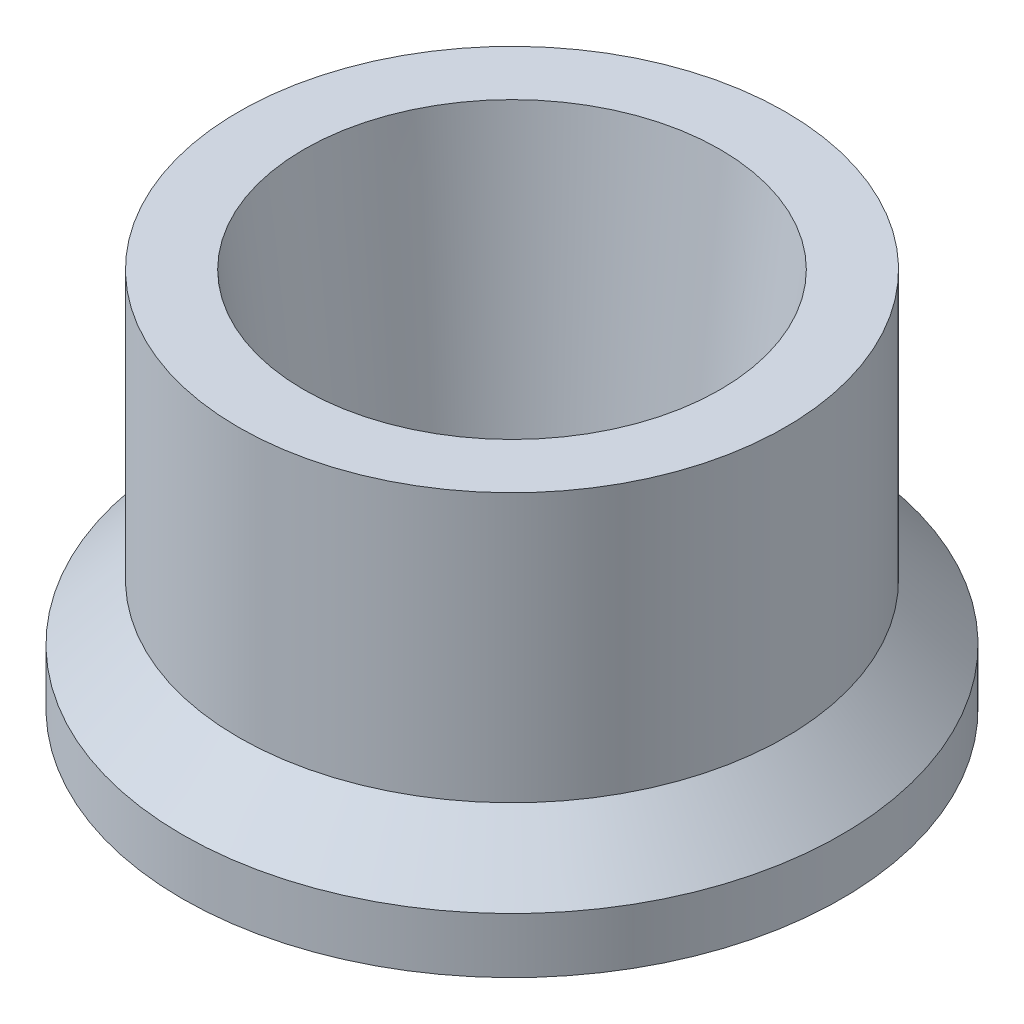
SolidWorks part; units mm, degrees
material "1060 Alloy"
ref_plane "Front" through (0, 0, 0) normal (0, 0, 1) x (1, 0, 0)
ref_plane "Top" through (0, 0, 0) normal (0, 1, 0) x (1, 0, 0)
ref_plane "Right" through (0, 0, 0) normal (1, 0, 0) x (0, 0, -1)
sketch "Sketch1" plane through (0, 0, 0) normal (0, 0, 1) x (1, 0, 0)
  line L0 (3.048, 0) -> (3.81, 6.9596)
  line L1 (50, 0) -> (-50, 0) construction
  line L2 (3.81, 6.9596) -> (5.0038, 6.9596)
  line L3 (5.0038, 6.9596) -> (5.0038, 2.0447)
  line L4 (5.0038, 2.0447) -> (6.0325, 1.016)
  line L5 (6.0325, 1.016) -> (6.0325, 0)
  line L6 (6.0325, 0) -> (3.048, 0)
  line L7 (0, 0) -> (0, 6.9596) construction
  line L8 (0, -50) -> (0, 50) construction
  dimension "D1" = 3.048
  dimension "D2" = 6.0325
  dimension "D3" = 5.0038
  dimension "D4" = 6.9596
  dimension "D5" = 1.016
  dimension "D6" = 45
  dimension "D7" = 3.81
revolve "Revolve1" add sketch "Sketch1" angle 360 about L7
